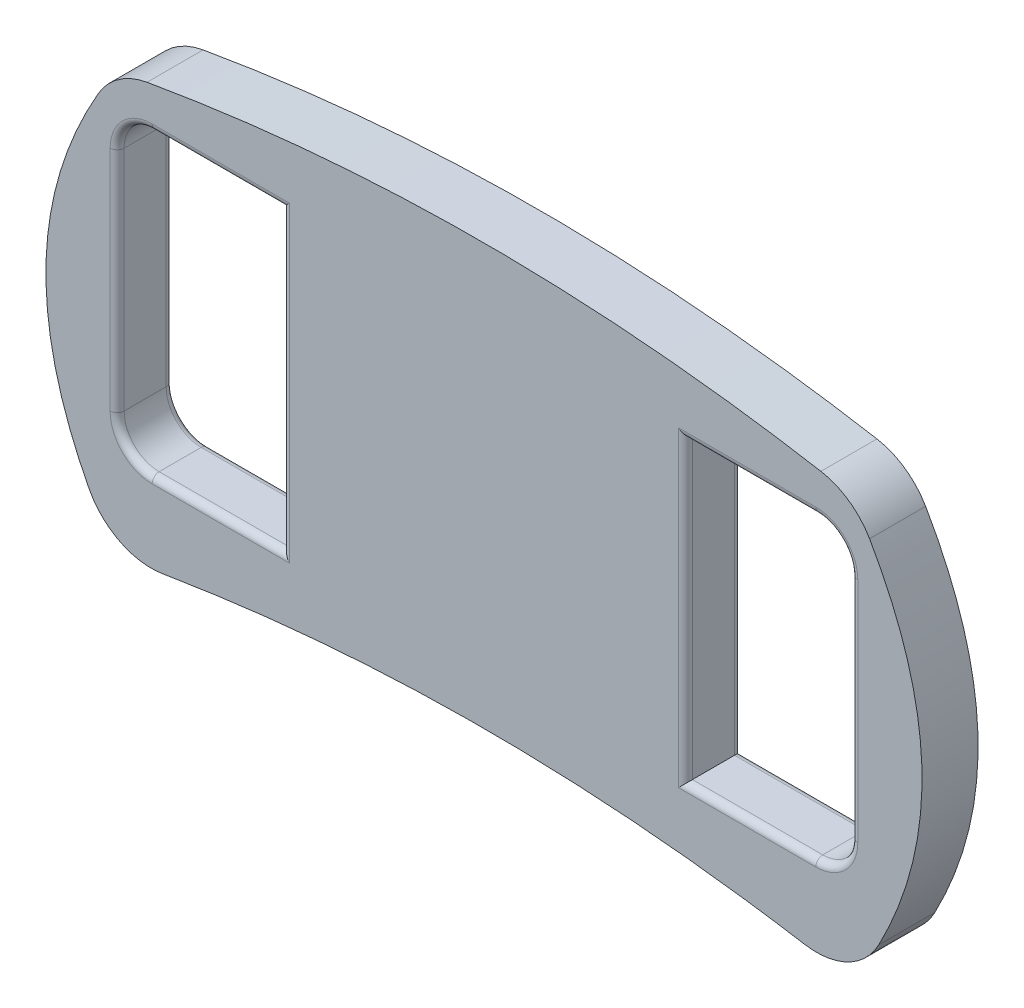
SolidWorks part; units mm, degrees
ref_plane "Front Plane" through (0, 0, 0) normal (0, 0, 1) x (1, 0, 0)
ref_plane "Top Plane" through (0, 0, 0) normal (0, 1, 0) x (1, 0, 0)
ref_plane "Right Plane" through (0, 0, 0) normal (1, 0, 0) x (0, 0, -1)
sketch "Sketch1" plane through (0, 0, 0) normal (0, 0, 1) x (1, 0, 0)
  line L0 (-131.1953, 32.7988) -> (135.5047, 32.7988) construction
  line L1 (2.1547, 32.7988) -> (2.1547, 45.4988) construction
  line L2 (-131.1953, 32.7988) -> (-131.1953, -119.6012) construction
  line L3 (-131.1953, -43.4012) -> (-156.5953, -43.4012) construction
  line L4 (135.5047, 32.7988) -> (135.5047, -119.6012) construction
  line L5 (135.5047, -43.4012) -> (160.9047, -43.4012) construction
  line L6 (-131.1953, -119.6012) -> (135.5047, -119.6012) construction
  line L7 (2.1547, -119.6012) -> (2.1547, -106.9012) construction
  line L8 (-131.1953, 11.6908) -> (135.5047, 11.6908) construction
  line L9 (135.5047, -103.0201) -> (-131.1953, -103.0201) construction
  line L10 (-131.1953, -79.0773) -> (135.5047, -79.0773) construction
  line L11 (-121.3337, 11.6908) -> (-121.3337, -79.0773) construction
  line L12 (-110.2557, 11.6908) -> (-88.0997, 11.6908)
  line L13 (-88.0997, 11.6908) -> (-88.0997, -79.0773)
  line L14 (-88.0997, -79.0773) -> (-110.6131, -79.0773)
  line L15 (118.0939, 11.6908) -> (118.0939, -79.0773) construction
  line L16 (118.0939, 2.7569) -> (106.9179, 2.7569) construction
  line L17 (106.9179, 11.6908) -> (84.8199, 11.6908)
  line L18 (84.8199, 11.6908) -> (84.8199, -79.0773)
  line L19 (84.8199, -79.0773) -> (106.9179, -79.0773)
  spline S0 degree 2 poles (-131.1953, 32.7988) (2.1547, 58.1988) (135.5047, 32.7988) knots 0 0 0 1 1 1
  spline S1 degree 2 poles (-131.1953, 32.7988) (-181.9953, -43.4012) (-131.1953, -119.6012) knots 0 0 0 1 1 1
  spline S2 degree 2 poles (135.5047, 32.7988) (186.3047, -43.4012) (135.5047, -119.6012) knots 0 0 0 1 1 1
  spline S3 degree 2 poles (-131.1953, -119.6012) (2.1547, -94.2012) (135.5047, -119.6012) knots 0 0 0 1 1 1
  spline S4 degree 2 poles (-110.2557, 11.6908) (-132.2328, -33.6122) (-110.6131, -79.0773) knots 0 0 0 1 1 1
  spline S5 degree 2 poles (106.9179, 11.6908) (129.2699, -33.6933) (106.9179, -79.0773) knots 0 0 0 1 1 1
  point P38 (0, 0)
  dimension "D13" = 23.9428
  dimension "D1" = 266.7
  dimension "D2" = 12.7
  dimension "D3" = 152.4
  dimension "D4" = 25.4
  dimension "D5" = 152.4
  dimension "D6" = 25.4
  dimension "D7" = 12.7
  dimension "D8" = 90.7681
  dimension "D9" = 22.156
  dimension "D10" = 11.078
  dimension "D11" = 11.176
  dimension "D12" = 22.098
  dimension "D14" = 88.0997
  dimension "D15" = 84.8199
extrude "Boss-Extrude2" add sketch "Sketch1" along normal blind 20.32 contours S0 S2 S3 S1
fillet "Fillet1" radius 25.4 1 edges at (135.5047, -119.6012, 10.16)
fillet "Fillet2" radius 25.4 1 edges at (-131.1953, -119.6012, 10.16)
fillet "Fillet3" radius 25.4 1 edges at (135.5047, 32.7988, 10.16)
fillet "Fillet4" radius 25.4 1 edges at (-131.1953, 32.7988, 10.16)
sketch "Sketch2" plane through (0, 0, 20.32) normal (0, 0, 1) x (1, 0, 0)
  line L0 (-156.1897, -33.7713) -> (-130.7897, -33.7713) construction
  line L1 (-118.0897, 20.1739) -> (-70.8457, 20.1739)
  line L2 (-130.7897, 7.4739) -> (-130.7897, -75.0165)
  line L3 (-118.0897, -87.7165) -> (-70.8457, -87.7165)
  line L4 (135.099, 7.4739) -> (135.099, -75.0165)
  line L5 (135.099, -33.7713) -> (160.499, -33.7713) construction
  line L6 (-118.0897, 20.1739) -> (-70.8457, 20.1739) construction
  line L7 (75.155, 20.1739) -> (122.399, 20.1739)
  line L9 (-70.8457, 20.1739) -> (-70.8457, -87.7165)
  line L11 (75.155, 20.1739) -> (75.155, -87.7165)
  line L12 (75.155, 20.1739) -> (122.399, 20.1739) construction
  line L13 (75.155, -87.7165) -> (122.399, -87.7165)
  arc A0 (122.399, 20.1739) -> (135.099, 7.4739) centre (122.399, 7.4739) cw
  arc A1 (-130.7897, -75.0165) -> (-118.0897, -87.7165) centre (-118.0897, -75.0165) ccw
  arc A2 (-118.0897, 20.1739) -> (-130.7897, 7.4739) centre (-118.0897, 7.4739) ccw
  arc A3 (122.399, -87.7165) -> (135.099, -75.0165) centre (122.399, -75.0165) ccw
  parabola Q0 (-137.5867, 22.5182) -> (-140.8945, -103.3112) focus (-99.4453, -43.4012) apex (-156.5953, -43.4012) construction
  parabola Q1 (141.8961, 22.5182) -> (145.2038, -103.3112) focus (103.7547, -43.4012) apex (160.9047, -43.4012) construction
  dimension "D2" = 12.7
  dimension "D1" = 25.4
  dimension "D4" = 82.4904
  dimension "D6" = 25.4
  dimension "D7" = 47.244
  dimension "D8" = 47.244
extrude "Cut-Extrude1" cut sketch "Sketch2" against normal blind 20.32 contours L1 L9 L3 A1 L2 A2 | L11 L13 A3 L4 A0 L7
fillet "Fillet5" radius 2.54 24 edges at (-94.4677, 20.1739, 20.32) (-127.0699, 16.4542, 20.32) (-94.4677, -87.7165, 20.32) (-127.0699, -83.9968, 20.32) (-130.7897, -33.7713, 20.32) (-70.8457, -33.7713, 0) (-94.4677, -87.7165, 0) (-127.0699, -83.9968, 0) (-130.7897, -33.7713, 0) (-127.0699, 16.4542, 0) (-94.4677, 20.1739, 0) (98.777, -87.7165, 0) (131.3793, -83.9968, 0) (135.099, -33.7713, 0) (131.3793, 16.4542, 0) (98.777, 20.1739, 0) (75.155, -33.7713, 0) (131.3793, -83.9968, 20.32) (98.777, -87.7165, 20.32) (98.777, 20.1739, 20.32) (131.3793, 16.4542, 20.32) (135.099, -33.7713, 20.32) (75.155, -33.7713, 20.32) (-70.8457, -33.7713, 20.32)
